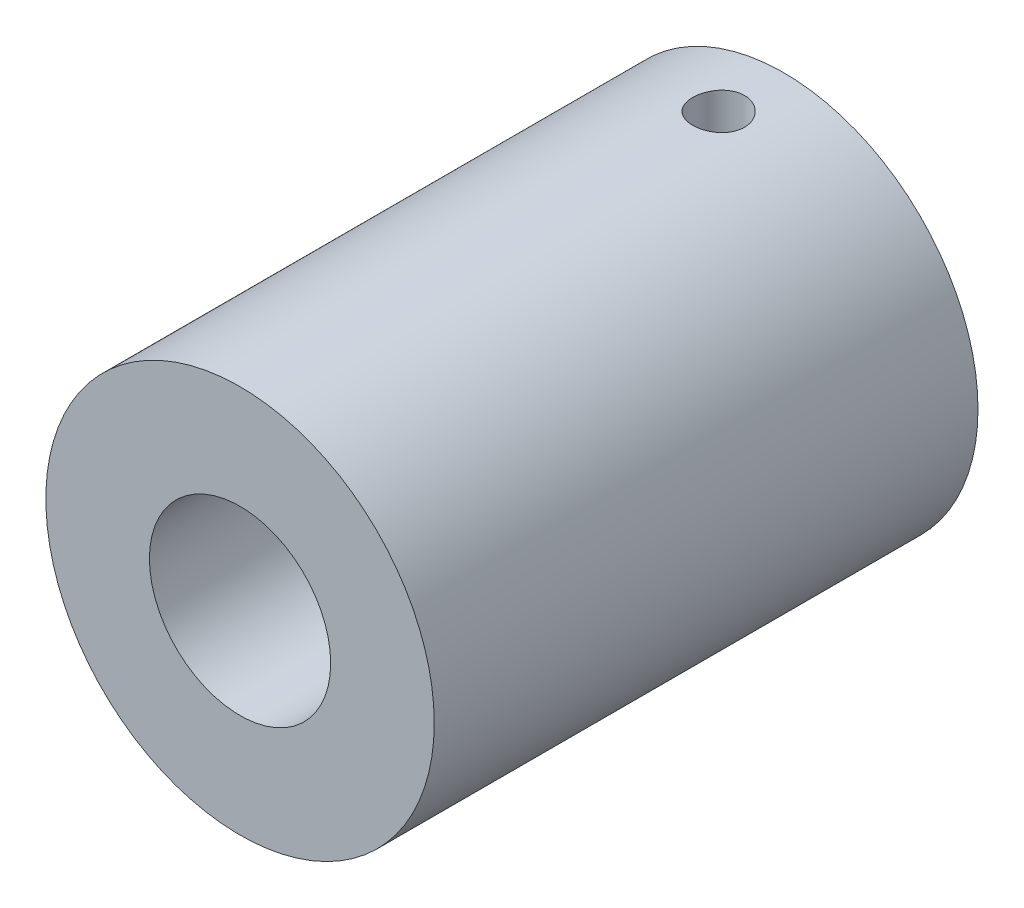
SolidWorks part; units mm, degrees
ref_plane "前视基准面" through (0, 0, 0) normal (0, 0, 1) x (1, 0, 0)
ref_plane "上视基准面" through (0, 0, 0) normal (0, 1, 0) x (1, 0, 0)
ref_plane "右视基准面" through (0, 0, 0) normal (1, 0, 0) x (0, 0, -1)
sketch "草图1" plane through (0, 0, 0) normal (0, 0, 1) x (1, 0, 0)
  circle A0 centre (0, -2.3735) radius 15
extrude "凸台-拉伸1" add sketch "草图1" along normal blind 42
sketch "草图2" plane through (0, 0, 42) normal (0, 0, 1) x (1, 0, 0)
  circle A0 centre (0, -2.3735) radius 7
extrude "切除-拉伸1" cut sketch "草图2" against normal blind 20
sketch "草图3" plane through (0, 0, 0) normal (0, 0, -1) x (-1, 0, 0)
  circle A0 centre (0, -2.3735) radius 5
extrude "切除-拉伸2" cut sketch "草图3" against normal blind 20
ref_plane "基准面1" through (0, 10, 0) normal (0, 1, 0) x (1, 0, 0)
sketch "草图5" plane through (0, 10, 0) normal (0, 1, 0) x (1, 0, 0)
  line L0 (0, 0) -> (0, -42) construction
  line L1 (-15, -42) -> (15, -42) construction
  circle A0 centre (0, -5.0371) radius 2
extrude "切除-拉伸3" cut sketch "草图5" along normal blind 20 and the other way blind 10
